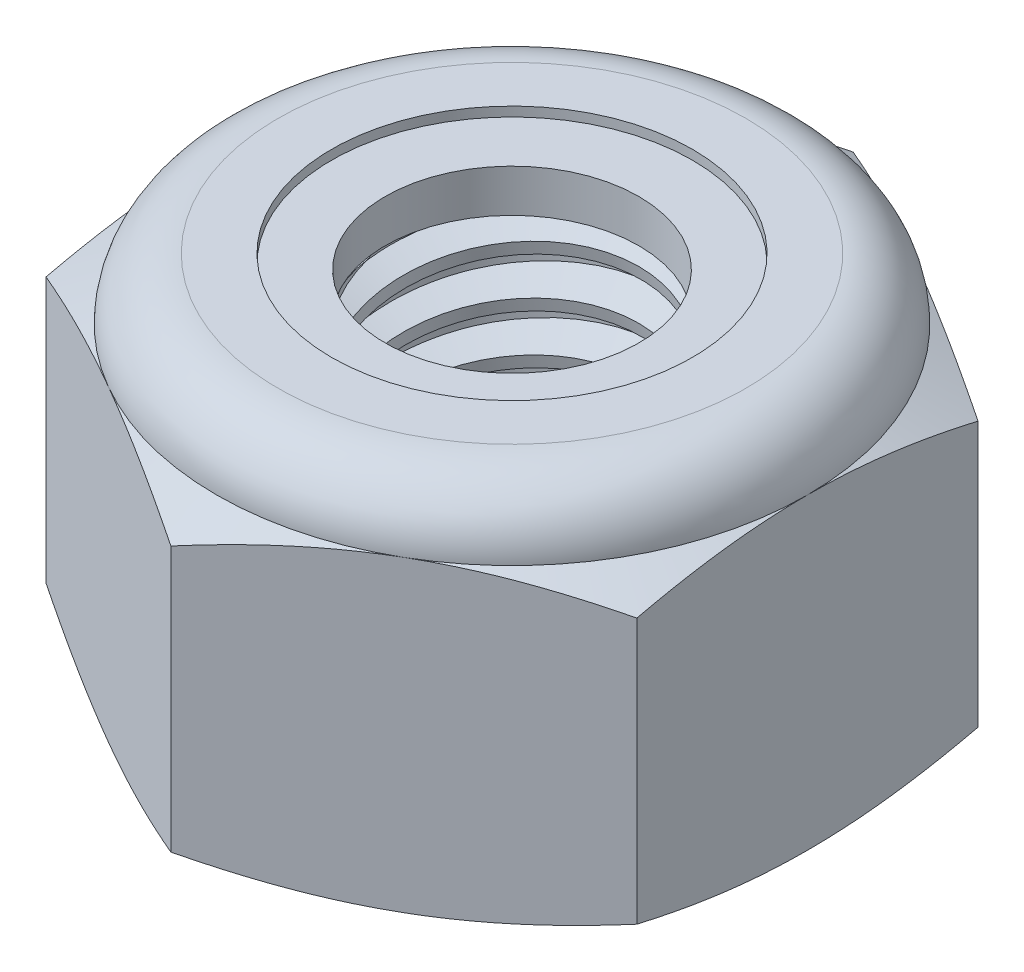
SolidWorks part; units mm, degrees
ref_plane "Front" through (0, 0, 0) normal (0, 0, 1) x (1, 0, 0)
ref_plane "Top" through (0, 0, 0) normal (0, 1, 0) x (1, 0, 0)
ref_plane "Right" through (0, 0, 0) normal (1, 0, 0) x (0, 0, -1)
sketch "Sketch1" plane through (0, 0, 0) normal (0, 1, 0) x (1, 0, 0)
  line L1 (0, 5.4993) -> (-4.7625, 2.7496)
  line L2 (-4.7625, 2.7496) -> (-4.7625, -2.7496)
  line L3 (-4.7625, -2.7496) -> (0, -5.4993)
  line L4 (0, -5.4993) -> (4.7625, -2.7496)
  line L5 (4.7625, -2.7496) -> (4.7625, 2.7496)
  line L6 (4.7625, 2.7496) -> (0, 5.4993)
  circle A0 centre (0, 0) radius 4.7625 construction
  dimension "Hex Flats" = 9.525
extrude "Extrude1" add sketch "Sketch1" along normal blind 5.9531
sketch "Sketch2" plane through (0, 0, 0) normal (1, 0, 0) x (0, 0, -1)
  line L0 (-2.413, 0) -> (-2.413, 5.9531) construction
  line L1 (0, 0) -> (2.413, 0)
  line L2 (0, 0) -> (0, 5.9531)
  line L3 (0, 5.9531) -> (2.413, 5.9531)
  line L4 (2.413, 0) -> (2.413, 5.9531)
  line L5 (-2.7496, 5.9531) -> (2.7496, 5.9531) construction
  line L7 (0, -2.413) -> (0, 0) construction
  dimension "Thread Dia" = 4.826
revolve "Revolve1" add sketch "Sketch2" angle 360 about L7
sketch "Sketch3" plane through (0, 0, 0) normal (1, 0, 0) x (0, 0, -1)
  line L0 (2.413, 5.9531) -> (-2.413, 5.9531) construction
  line L1 (-2.413, 5.9531) -> (-2.413, 5.1594) construction
  line L2 (-2.413, 5.1594) -> (2.413, 5.9531) construction
  line L3 (2.413, 5.9531) -> (2.4291, 5.8552) construction
  line L4 (2.4291, 5.8552) -> (2.5418, 5.1699)
  line L5 (2.5418, 5.1699) -> (2.0776, 5.3449)
  line L6 (2.0776, 5.3449) -> (2.0454, 5.5407)
  line L7 (2.0454, 5.5407) -> (2.4291, 5.8552)
  line L8 (2.0615, 5.4428) -> (2.4855, 5.5126) construction
  line L9 (2.413, 5.9531) -> (2.413, 5.5006) construction
  line L10 (2.413, 5.5006) -> (-2.413, 4.7069) construction
  line L11 (-2.413, 4.7069) -> (-2.413, 5.1594) construction
  line L12 (-0.1397, 5.9531) -> (0.1397, 4.2544) construction
  line L13 (-2.413, 0) -> (-2.413, 5.9531) construction
  line L14 (0, 5.9531) -> (2.413, 5.9531) construction
  line L15 (2.413, 0) -> (2.413, 5.9531) construction
  point P13 (0, 5.1038)
revolve "Cut-Revolve1" cut sketch "Sketch3" angle 360 about L12
pattern_linear "LPattern1" count 8 spacing 0.7937 along (0, -1, 0) count 2 spacing 0.7937 along (0, 1, 0) of "Cut-Revolve1"
sketch "Sketch4" plane through (0, 0, 0) normal (1, 0, 0) x (0, 0, -1)
  line L0 (0, 5.9531) -> (2.413, 5.9531)
  line L1 (2.413, 5.9531) -> (2.0454, 5.7817)
  line L2 (2.0454, 5.7817) -> (2.0454, 0.1714)
  line L3 (2.0454, 0.1714) -> (2.413, 0)
  line L4 (2.413, 0) -> (0, 0)
  line L5 (0, 0) -> (0, 5.9531)
  line L6 (2.413, 0) -> (2.413, 5.9531) construction
  line L7 (0, 5.9531) -> (2.413, 5.9531) construction
  line L8 (0, 0) -> (2.413, 0) construction
  line L9 (0, 0) -> (0, 5.9531) construction
  line L10 (0, 5.9531) -> (0, 6.3587) construction
  dimension "D1" = 25
revolve "Cut-Revolve2" cut sketch "Sketch4" angle 360 about L10
combine bodies "Combine1" operation type subtract main body 112 bodies to subtract 111
sketch "Sketch5" plane through (0, 0, 0) normal (1, 0, 0) x (0, 0, -1)
  line L0 (0, 0) -> (4.7625, 0)
  line L1 (4.7625, 0) -> (5.4993, 0.3436)
  line L2 (5.4993, 0.3436) -> (5.4993, 4.6174)
  line L3 (5.4993, 4.6174) -> (4.7625, 4.9609)
  line L4 (3.7703, 5.9531) -> (3.7703, 7.2231)
  line L5 (3.7703, 7.2231) -> (6.7693, 7.2231)
  line L6 (6.7693, 7.2231) -> (6.7693, -1.27)
  line L7 (6.7693, -1.27) -> (0, -1.27)
  line L8 (0, -1.27) -> (0, 0)
  line L9 (4.7625, 4.9609) -> (4.7625, 0) construction
  line L10 (0, 0) -> (2.413, 0) construction
  line L13 (5.4993, 2.4805) -> (6.7693, 2.4805) construction
  line L14 (5.4993, 5.9531) -> (5.4993, 0) construction
  line L15 (0, 0) -> (0, 7.2231) construction
  line L20 (0, 7.2231) -> (3.7703, 7.2231) construction
  line L22 (0, 5.9531) -> (2.413, 5.9531) construction
  arc A0 (4.7625, 4.9609) -> (3.7703, 5.9531) centre (3.7703, 4.9609) ccw
revolve "Cut-Revolve3" cut sketch "Sketch5" angle 360 about L15
sketch "Sketch6" plane through (0, 0, 0) normal (1, 0, 0) x (0, 0, -1)
  line L0 (0, 4.9609) -> (4.6101, 4.9609)
  line L1 (3.7703, 5.8007) -> (2.9079, 5.8007)
  line L2 (0, 7.2231) -> (0, 4.9609)
  line L3 (2.9079, 7.2231) -> (0, 7.2231)
  line L4 (0, 7.2231) -> (3.7703, 7.2231) construction
  line L5 (0, 0) -> (0, 7.2231) construction
  line L6 (0, 7.2231) -> (0, 44.323) construction
  line L7 (2.9079, 5.8007) -> (2.9079, 7.2231)
  line L8 (3.7703, 5.9531) -> (3.7703, 5.8007) construction
  line L9 (2.9079, 5.8007) -> (2.0454, 5.8007) construction
  line L10 (2.0454, 5.8007) -> (2.0454, 5.7817) construction
  arc A0 (4.6101, 4.9609) -> (3.7703, 5.8007) centre (3.7703, 4.9609) ccw
  arc A1 (4.7625, 4.9609) -> (3.7703, 5.9531) centre (3.7703, 4.9609) ccw construction
  dimension "D1" = 0.1524
revolve "Cut-Revolve4" cut sketch "Sketch6" angle 360 about L6
sketch "Sketch7" plane through (0, 0, 0) normal (1, 0, 0) x (0, 0, -1)
  line L0 (2.0454, 5.0371) -> (4.5301, 5.0371)
  line L1 (3.7703, 5.7245) -> (2.0454, 5.7245)
  line L2 (2.0454, 5.7245) -> (2.0454, 5.0371)
  line L3 (2.0454, 5.0371) -> (0, 5.0371) construction
  line L4 (0, 5.0371) -> (0, 5.7245) construction
  line L5 (0, 5.7245) -> (2.0454, 5.7245) construction
  line L6 (2.0454, 5.0371) -> (2.0454, 4.9609) construction
  line L7 (0, 4.9609) -> (4.6101, 4.9609) construction
  line L8 (3.7703, 5.7245) -> (3.7703, 5.8007) construction
  arc A0 (4.5301, 5.0371) -> (3.7703, 5.7245) centre (3.7703, 4.9609) ccw
  arc A2 (4.6101, 4.9609) -> (3.7703, 5.8007) centre (3.7703, 4.9609) ccw construction
  dimension "D1" = 0.0762
revolve "Revolve2" add sketch "Sketch7" angle 360 about L4
equation "\"D1@Sketch3\"=\"Thread Pitch@Sketch3\"/8"
equation "\"D2@Sketch3\"=\"Thread Pitch@Sketch3\"/4"
equation "\"D5@Sketch3\"=\"Thread Pitch@Sketch3\""
equation "\"D4@LPattern1\"=\"Thread Pitch@Sketch3\""
equation "\"D3@LPattern1\"=\"Thread Pitch@Sketch3\""
equation "\"D1@LPattern1\"=\"Height@Extrude1\"/\"Thread Pitch@Sketch3\""
equation "\"D4@Sketch5\"=\"Height@Extrude1\"/6"
